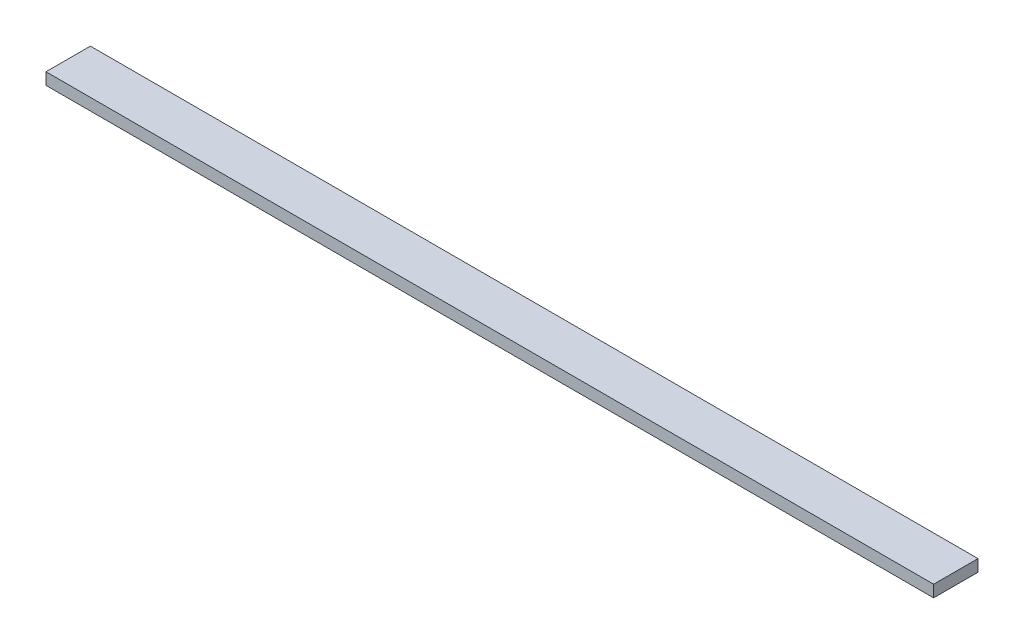
SolidWorks part; units mm, degrees
ref_plane "Спереди" through (0, 0, 0) normal (0, 0, 1) x (1, 0, 0)
ref_plane "Сверху" through (0, 0, 0) normal (0, 1, 0) x (1, 0, 0)
ref_plane "Справа" through (0, 0, 0) normal (1, 0, 0) x (0, 0, -1)
sketch "Эскиз1" plane through (0, 0, 0) normal (0, 1, 0) x (1, 0, 0)
  line L1 (-300, 15) -> (300, 15)
  line L2 (-300, 15) -> (-300, -15)
  line L3 (-300, -15) -> (300, -15)
  line L4 (300, 15) -> (300, -15)
  line L5 (-300, 15) -> (300, -15) construction
  line L6 (-300, -15) -> (300, 15) construction
  point P0 (0, 0)
extrude "Бобышка-Вытянуть1" add sketch "Эскиз1" along normal blind 8
